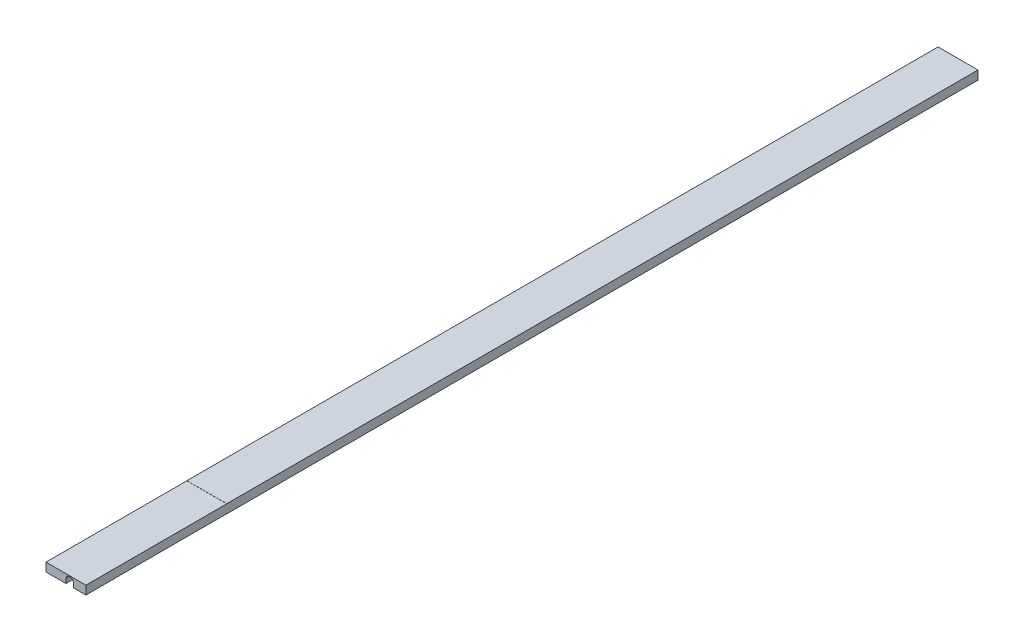
SolidWorks part; units mm, degrees
material "CFOAM 20"
ref_plane "Front Plane" through (0, 0, 0) normal (0, 0, 1) x (1, 0, 0)
ref_plane "Top Plane" through (0, 0, 0) normal (0, 1, 0) x (1, 0, 0)
ref_plane "Right Plane" through (0, 0, 0) normal (1, 0, 0) x (0, 0, -1)
sketch "Sketch1" plane through (0, 0, 0) normal (0, 0, 1) x (1, 0, 0)
  line L1 (-12.5, 2.75) -> (12.5, 2.75)
  line L2 (-12.5, 2.75) -> (-12.5, -2.75)
  line L3 (-12.5, -2.75) -> (12.5, -2.75)
  line L4 (12.5, 2.75) -> (12.5, -2.75)
  line L5 (-12.5, 2.75) -> (12.5, -2.75) construction
  line L6 (-12.5, -2.75) -> (12.5, 2.75) construction
  point P0 (0, 0)
  dimension "D1" = 25
  dimension "D2" = 5.5
extrude "Extrude1" add sketch "Sketch1" along normal mid plane 518.8
sketch "Sketch6" plane through (0, 2.75, 0) normal (0, 1, 0) x (1, 0, 0)
  line L0 (12.5, -259.4) -> (12.5, 259.4) construction
  line L1 (-12.5, 259.4) -> (12.5, 259.4)
  line L2 (-12.5, 259.4) -> (-12.5, 279.4)
  line L3 (-12.5, 279.4) -> (12.5, 279.4)
  line L4 (12.5, 259.4) -> (12.5, 279.4)
  line L5 (-12.5, -259.4) -> (12.5, -259.4)
  line L6 (-12.5, -259.4) -> (-12.5, -279.4)
  line L7 (-12.5, -279.4) -> (12.5, -279.4)
  line L8 (12.5, -259.4) -> (12.5, -279.4)
  dimension "D1" = 20
  dimension "D2" = 20
extrude "Boss-Extrude2" add sketch "Sketch6" against normal up to surface (5.5 mm away) up to face at (0, -2.75, 0)
sketch "Sketch7" plane through (0, 0, 279.4) normal (0, 0, 1) x (1, 0, 0)
  line L0 (2.381, -0.1278) -> (-12.5, -0.1278) construction
  line L1 (-12.5, -2.75) -> (-12.5, 2.75) construction
  line L2 (-12.5, 2.75) -> (12.5, 2.75) construction
  line L3 (12.5, -2.75) -> (-12.5, -2.75) construction
  line L4 (-0.0003, -0.1278) -> (-0.0003, -2.75)
  line L5 (-0.0003, -2.75) -> (4.7622, -2.75)
  line L6 (4.7622, -2.75) -> (4.7622, -0.1278)
  arc A0 (4.7622, -0.1278) -> (-0.0003, -0.1278) centre (2.381, -0.1278) ccw
  dimension "D1" = 4.7625
  dimension "D2" = 14.881
  dimension "D3" = 2.8778
extrude "Cut-Extrude2" cut sketch "Sketch7" against normal through all
sketch "Sketch8" plane through (-12.5, 0, 0) normal (-1, 0, 0) x (0, 0, 1)
  line L0 (191.15, 2.6814) -> (191.15, -2.6814) construction
  line L1 (279.4, 2.75) -> (191.15, 2.75)
  line L2 (279.4, 2.75) -> (279.4, 2.6814)
  line L3 (279.4, 2.6814) -> (191.15, 2.6814)
  line L4 (191.15, 2.75) -> (191.15, 2.6814)
  line L5 (279.4, -2.75) -> (191.15, -2.75)
  line L6 (279.4, -2.75) -> (279.4, -2.6814)
  line L7 (279.4, -2.6814) -> (191.15, -2.6814)
  line L8 (191.15, -2.75) -> (191.15, -2.6814)
  dimension "D1" = 88.25
  dimension "D2" = 0.0686
  dimension "D3" = 0.0686
extrude "Cut-Extrude3" cut sketch "Sketch8" against normal through all
